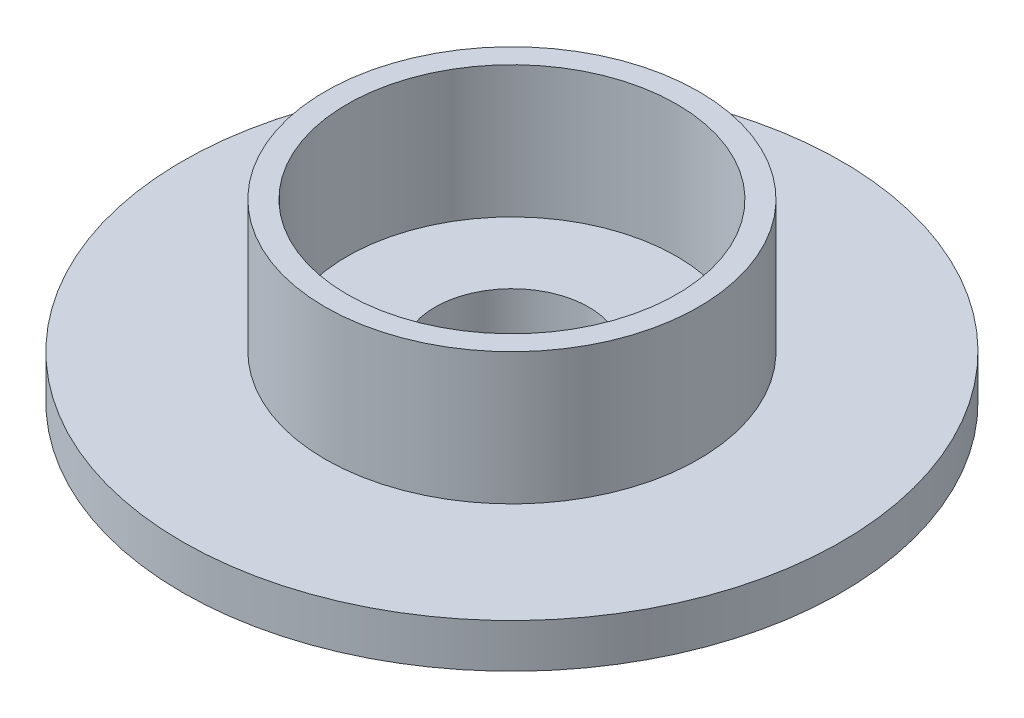
SolidWorks part; units mm, degrees
ref_plane "Front" through (0, 0, 0) normal (0, 0, 1) x (1, 0, 0)
ref_plane "Top" through (0, 0, 0) normal (0, 1, 0) x (1, 0, 0)
ref_plane "Right" through (0, 0, 0) normal (1, 0, 0) x (0, 0, -1)
sketch "Sketch1" plane through (0, 0, 0) normal (0, 1, 0) x (1, 0, 0)
  circle A0 centre (-26.5502, 13.5076) radius 75
  dimension "D1" = 150
extrude "Boss-Extrude1" add sketch "Sketch1" along normal blind 10
sketch "Sketch2" plane through (0, 10, 0) normal (0, 1, 0) x (1, 0, 0)
  circle A0 centre (-26.5502, 13.5076) radius 37.5
  circle A1 centre (-26.5502, 13.5076) radius 42.5
  dimension "D1" = 75
  dimension "D2" = 5
extrude "Boss-Extrude2" add sketch "Sketch2" along normal blind 30 contours A1 | A0
sketch "Sketch4" plane through (0, 10, 0) normal (0, 1, 0) x (1, 0, 0)
  circle A0 centre (-26.5502, 13.5076) radius 17.5
  dimension "D1" = 35
extrude "Cut-Extrude2" cut sketch "Sketch4" against normal through all contours A0
sketch "Text-Lucas Lim" plane through (0, 10, 0) normal (0, 1, 0) x (1, 0, 0)
  text T0 "<b>Lucas Lim</b>"
